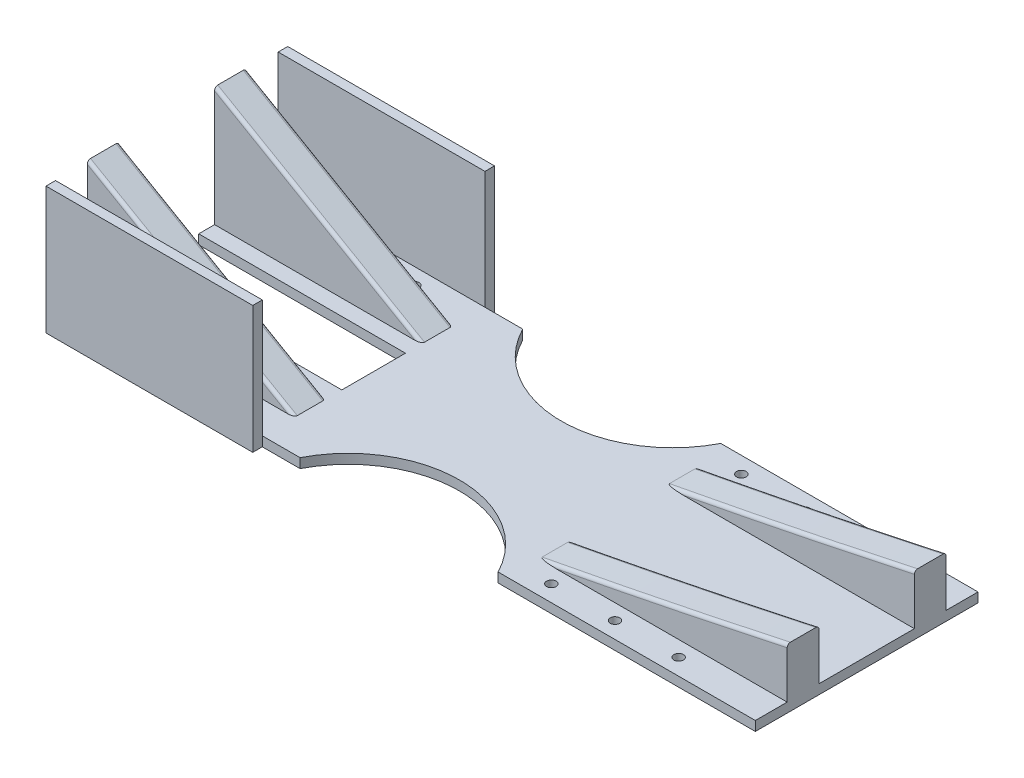
SolidWorks part; units mm, degrees
ref_plane "前视基准面" through (0, 0, 0) normal (0, 0, 1) x (1, 0, 0)
ref_plane "上视基准面" through (0, 0, 0) normal (0, 1, 0) x (1, 0, 0)
ref_plane "右视基准面" through (0, 0, 0) normal (1, 0, 0) x (0, 0, -1)
sketch "草图1" plane through (0, 0, 0) normal (0, 1, 0) x (1, 0, 0)
  line L0 (-92.9537, 0) -> (133.3808, 0) construction
  line L1 (0, 79.573) -> (0, -79.8577) construction
  line L2 (-82.7046, -35) -> (-82.7046, 35)
  line L3 (-82.7046, 35) -> (137.2954, 35)
  line L4 (137.2954, 35) -> (137.2954, -35)
  line L5 (-82.7046, -35) -> (137.2954, -35)
  point P10 (137.2954, 0)
  point P11 (-82.7046, 0)
  dimension "D1" = 70
  dimension "D2" = 220
extrude "凸台-拉伸1" add sketch "草图1" along normal blind 3
sketch "草图2" plane through (0, 0, 0) normal (0, 0, 1) x (1, 0, 0)
  line L0 (-2.7046, 3) -> (-2.7046, 43.2178) construction
  line L2 (59.2954, 3) -> (59.2954, 47.8617) construction
  line L3 (-82.7046, 3) -> (-82.7046, 0) construction
  line L5 (-82.7046, 40.5278) -> (-82.7046, 3)
  line L7 (137.2954, 3) -> (137.2954, 18.8104)
  line L8 (59.2954, 3) -> (137.2954, 3)
  line L10 (-82.7046, 3) -> (-17.7046, 3)
  line L11 (-82.7046, 40.5278) -> (-17.7046, 3)
  spline S0 degree 2 poles (59.2954, 3) (98.4061, 10.3571) (137.2954, 18.8104) knots 0 0 0 1 1 1
  dimension "D1" = 62
  dimension "D2" = 80
  dimension "D3" = 30
  dimension "D4" = 65
extrude "凸台-拉伸2" add sketch "草图2" along normal blind 25 and the other way blind 25
sketch "草图6" plane through (-82.7046, 0, 0) normal (-1, 0, 0) x (0, 0, 1)
  line L0 (0, 40.5278) -> (0, 0) construction
  line L1 (-25, 40.5278) -> (25, 40.5278) construction
  line L2 (-15, 40.5278) -> (-15, 3)
  line L3 (-15, 3) -> (15, 3)
  line L4 (15, 3) -> (15, 40.5278)
  line L5 (15, 40.5278) -> (-15, 40.5278)
  dimension "D1" = 15
  dimension "D2" = 15
extrude "切除-拉伸4" cut sketch "草图6" against normal through all
ref_plane "基准面1" through (-87.2964, 23.391, 0) normal (-0.9659, 0.2588, 0) x (0, 0, 1)
sketch "草图7" plane through (0, 3, 0) normal (0, 1, 0) x (1, 0, 0)
  line L0 (-2.7046, 35) -> (-2.7046, -35) construction
  line L4 (137.2954, 35) -> (-82.7046, 35) construction
  line L5 (-82.7046, -35) -> (137.2954, -35) construction
  line L6 (-82.7046, 35) -> (-82.7046, 25) construction
  line L7 (53.2954, 35) -> (53.2954, -35) construction
  line L8 (25.2954, 88.1076) -> (25.2954, -100.7895) construction
  line L9 (-82.7046, 0) -> (117.2954, 0) construction
  line L11 (-82.7046, 15) -> (-82.7046, -15) construction
  circle A0 centre (25.2954, 51) radius 35
  circle A1 centre (25.2954, -51) radius 35
  dimension "D4" = 70
  dimension "D1" = 80
  dimension "D2" = 56
  dimension "D3" = 28
  dimension "D5" = 102
extrude "切除-拉伸5" cut sketch "草图7" against normal through all
sketch "草图8" plane through (-82.7046, 0, 0) normal (-1, 0, 0) x (0, 0, 1)
  line L0 (35, 0) -> (35, 40)
  line L1 (35, 40) -> (38, 40)
  line L2 (38, 40) -> (38, 0)
  line L3 (38, 0) -> (35, 0)
  line L4 (0, 36.5043) -> (0, -13.2047) construction
  line L5 (-38, 0) -> (-35, 0)
  line L6 (-38, 40) -> (-38, 0)
  line L7 (-35, 40) -> (-38, 40)
  line L8 (-35, 0) -> (-35, 40)
  dimension "D1" = 3
  dimension "D2" = 40
extrude "凸台-拉伸3" add sketch "草图8" against normal blind 65
sketch "草图9" plane through (0, 3, 0) normal (0, 1, 0) x (1, 0, 0)
  line L0 (-82.7046, 15) -> (-82.7046, -15) construction
  line L1 (-82.7046, 0) -> (117.2954, 0) construction
  circle A0 centre (-74.7668, 29.8601) radius 1.5
  circle A1 centre (-54.7668, 29.8601) radius 1.5
  circle A2 centre (-34.7668, 29.8601) radius 1.5
  circle A3 centre (-34.7668, -29.8601) radius 1.5
  circle A4 centre (-54.7668, -29.8601) radius 1.5
  circle A5 centre (-74.7668, -29.8601) radius 1.5
  circle A12 centre (68.0316, 29.8601) radius 1.5
  circle A13 centre (88.0316, 29.8601) radius 1.5
  circle A14 centre (108.0316, 29.8601) radius 1.5
  circle A15 centre (108.0316, -29.8601) radius 1.5
  circle A16 centre (88.0316, -29.8601) radius 1.5
  circle A17 centre (68.0316, -29.8601) radius 1.5
  dimension "D1" = 3
  dimension "D5" = 3
  dimension "D2" = 3
  dimension "D6" = 3
extrude "切除-拉伸6" cut sketch "草图9" against normal through all
fillet "圆角5" radius 1 8 edges at (-50.2046, 21.7639, -15) (-50.2046, 21.7639, 15) (-50.2046, 21.7639, 25) (-50.2046, 21.7639, -25)
sketch "草图10" plane through (0, 3, 0) normal (0, 1, 0) x (1, 0, 0)
  line L0 (-82.7046, 0) -> (137.2954, 0) construction
  line L1 (-82.7046, 15) -> (-82.7046, -15) construction
  line L2 (137.2954, 15) -> (137.2954, -15) construction
  line L3 (-82.7046, -10) -> (-82.7046, 10)
  line L4 (-82.7046, 10) -> (-17.7046, 10)
  line L5 (-17.7046, 10) -> (-17.7046, -10)
  line L6 (-82.7046, -10) -> (-17.7046, -10)
  point P11 (-17.7046, 0)
  dimension "D1" = 20
extrude "切除-拉伸7" cut sketch "草图10" against normal through all
